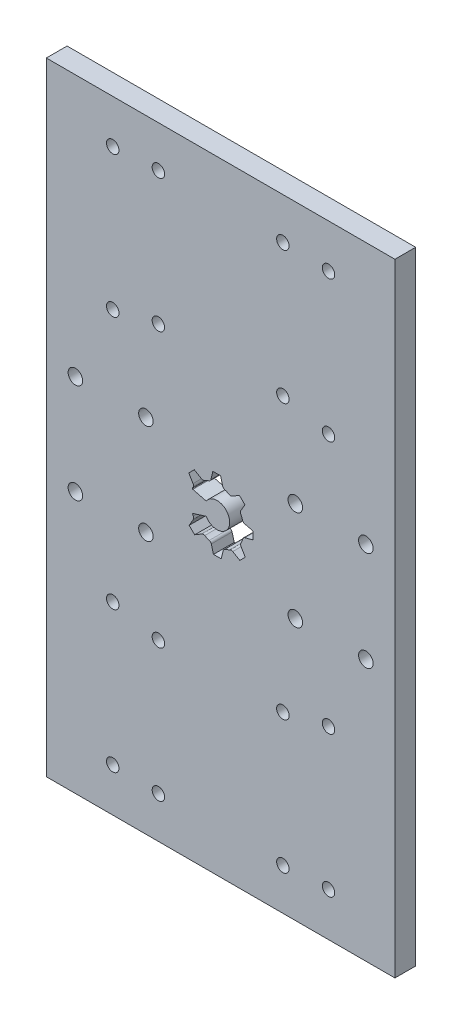
SolidWorks part; units mm, degrees
ref_plane "Alzado" through (0, 0, 0) normal (0, 0, 1) x (1, 0, 0)
ref_plane "Planta" through (0, 0, 0) normal (0, 1, 0) x (1, 0, 0)
ref_plane "Vista lateral" through (0, 0, 0) normal (1, 0, 0) x (0, 0, -1)
sketch "Croquis1" plane through (0, 0, 0) normal (0, 0, 1) x (1, 0, 0)
  line L0 (0, 0) -> (84, 0)
  line L1 (84, 0) -> (84, 150)
  line L2 (84, 150) -> (0, 150)
  line L3 (0, 150) -> (0, 0)
  line L4 (0, 75) -> (84, 75) construction
  line L5 (42, 150) -> (42, 0) construction
  line L6 (16, 122.5) -> (16, 139.5) construction
  line L7 (11, 122.5) -> (21, 122.5) construction
  line L8 (34.3233, 80.5616) -> (35.6367, 81.8973)
  line L9 (40.126, 83.8012) -> (41.9992, 83.8169)
  line L10 (46.5199, 81.9888) -> (47.8555, 80.6754)
  line L11 (49.7595, 76.1861) -> (49.7752, 74.3129)
  line L12 (47.9471, 69.7923) -> (46.6337, 68.4566)
  line L13 (35.3448, 72.6248) -> (38.5192, 73.6055)
  line L14 (34.3233, 80.5616) -> (35.3551, 78.8554)
  line L15 (42.1444, 66.5527) -> (40.2712, 66.5369)
  line L16 (35.7505, 68.3651) -> (34.4149, 69.6785)
  line L17 (35.6367, 81.8973) -> (37.3601, 80.8943)
  line L18 (40.126, 83.8012) -> (39.6491, 81.8651)
  line L19 (41.9992, 83.8169) -> (42.5086, 81.8892)
  line L20 (46.5199, 81.9888) -> (44.8137, 80.957)
  line L21 (47.8555, 80.6754) -> (46.8526, 78.9521)
  line L22 (49.7595, 76.1861) -> (47.8234, 76.663)
  line L23 (49.7752, 74.3129) -> (47.8474, 73.8035)
  line L24 (47.9471, 69.7923) -> (46.9153, 71.4985)
  line L25 (46.6337, 68.4566) -> (44.9103, 69.4595)
  line L26 (42.1444, 66.5527) -> (42.6213, 68.4887)
  line L27 (40.2712, 66.5369) -> (39.7618, 68.4647)
  line L28 (35.7505, 68.3651) -> (37.4568, 69.3969)
  line L29 (34.4149, 69.6785) -> (35.4178, 71.4018)
  line L30 (38.5418, 76.7854) -> (35.3058, 77.6293)
  circle A22 centre (27, 108) radius 1.5
  circle A23 centre (57, 108) radius 1.5
  circle A24 centre (16, 139.5) radius 1.5
  circle A25 centre (16, 105.5) radius 1.5
  circle A26 centre (68, 105.5) radius 1.5
  circle A27 centre (68, 139.5) radius 1.5
  circle A28 centre (68, 44.5) radius 1.5
  circle A29 centre (68, 10.5) radius 1.5
  circle A30 centre (16, 10.5) radius 1.5
  circle A31 centre (16, 44.5) radius 1.5
  circle A32 centre (7, 87) radius 1.75
  circle A33 centre (24, 87) radius 1.75
  circle A34 centre (24, 63) radius 1.75
  circle A35 centre (7, 63) radius 1.75
  circle A36 centre (60, 63) radius 1.75
  circle A37 centre (60, 87) radius 1.75
  circle A38 centre (77, 63) radius 1.75
  circle A39 centre (77, 87) radius 1.75
  circle A40 centre (27, 140) radius 1.5
  circle A41 centre (57, 140) radius 1.5
  circle A42 centre (57, 42) radius 1.5
  circle A43 centre (27, 42) radius 1.5
  circle A44 centre (57, 10) radius 1.5
  circle A45 centre (27, 10) radius 1.5
  arc A46 (43.1019, 69.0026) -> (44.2069, 69.4712) centre (41.1352, 75.1769) ccw
  arc A47 (35.2622, 72.4386) -> (35.4295, 72.1053) centre (41.1352, 75.1769) ccw
  arc A48 (35.3448, 72.6248) -> (35.2622, 72.4386) centre (35.3847, 72.4957) ccw
  arc A49 (35.2165, 77.815) -> (35.3058, 77.6293) centre (35.3399, 77.76) ccw
  arc A50 (38.0635, 80.8826) -> (37.3601, 80.8943) centre (37.7222, 81.5166) cw
  arc A51 (35.3786, 78.1522) -> (35.3551, 78.8554) centre (34.739, 78.4828) ccw
  arc A52 (42.9977, 81.3835) -> (42.5086, 81.8892) centre (43.2047, 82.0731) cw
  arc A53 (39.1685, 81.3513) -> (39.6491, 81.8651) centre (38.95, 82.0373) ccw
  arc A54 (46.8409, 78.2486) -> (46.8526, 78.9521) centre (47.4749, 78.5899) cw
  arc A55 (44.1105, 80.9335) -> (44.8137, 80.957) centre (44.4411, 81.5731) ccw
  arc A56 (47.3418, 73.3144) -> (47.8474, 73.8035) centre (48.0314, 73.1074) cw
  arc A57 (47.3096, 77.1436) -> (47.8234, 76.663) centre (47.9956, 77.3621) ccw
  arc A58 (44.2069, 69.4712) -> (44.9103, 69.4595) centre (44.5482, 68.8372) cw
  arc A59 (46.8918, 72.2016) -> (46.9153, 71.4985) centre (47.5314, 71.8711) ccw
  arc A60 (39.2727, 68.9704) -> (39.7618, 68.4647) centre (39.0657, 68.2808) cw
  arc A61 (43.1019, 69.0026) -> (42.6213, 68.4887) centre (43.3204, 68.3165) ccw
  arc A62 (35.4295, 72.1053) -> (35.4178, 71.4018) centre (34.7955, 71.764) cw
  arc A63 (38.1599, 69.4204) -> (37.4568, 69.3969) centre (37.8293, 68.7807) ccw
  arc A64 (38.1599, 69.4204) -> (39.2727, 68.9704) centre (41.1352, 75.1769) ccw
  arc A65 (35.3786, 78.1522) -> (35.2165, 77.815) centre (41.1352, 75.1769) ccw
  arc A66 (39.1685, 81.3513) -> (38.0635, 80.8826) centre (41.1352, 75.1769) ccw
  arc A67 (44.1105, 80.9335) -> (42.9977, 81.3835) centre (41.1352, 75.1769) ccw
  arc A68 (47.3096, 77.1436) -> (46.8409, 78.2486) centre (41.1352, 75.1769) ccw
  arc A69 (46.8918, 72.2016) -> (47.3418, 73.3144) centre (41.1352, 75.1769) ccw
  arc A70 (38.5192, 73.6055) -> (38.5418, 76.7854) centre (41.1352, 75.1769) ccw
  dimension "D3" = 16
  dimension "D7" = 10
  dimension "D8" = 7
  dimension "D5" = 17
  dimension "D12" = 12
  dimension "D6" = 3
  dimension "D9" = 3.5
  dimension "D10" = 3.5
  dimension "D13" = 3
  dimension "D16" = 3
  dimension "D18" = 0.1351
  dimension "D19" = 0.1351
  dimension "D1" = 84
  dimension "D2" = 150
  dimension "D4" = 47.5
  dimension "D11" = 17
  dimension "D14" = 10
  dimension "D15" = 15
  dimension "D17" = 32
extrude "Saliente-Extruir1" add sketch "Croquis1" along normal blind 5
